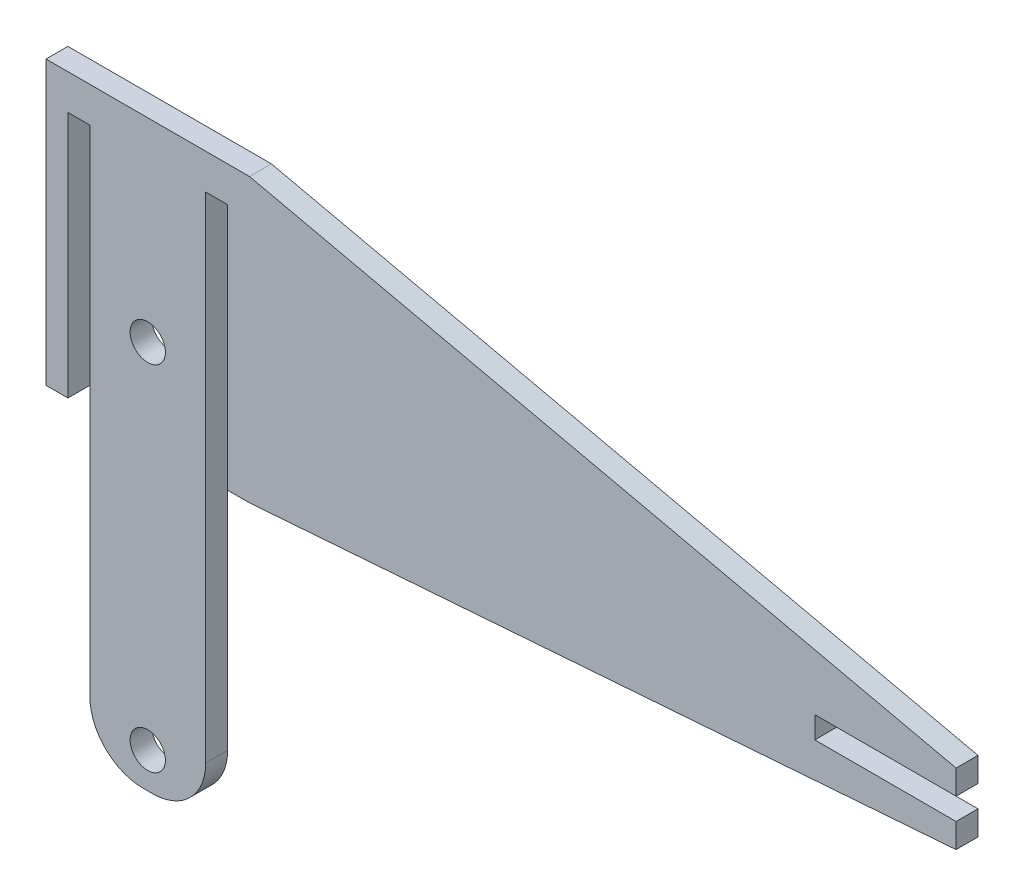
SolidWorks part; units mm, degrees
material "Teak"
ref_plane "Front Plane" through (0, 0, 0) normal (0, 0, 1) x (1, 0, 0)
ref_plane "Top Plane" through (0, 0, 0) normal (0, 1, 0) x (1, 0, 0)
ref_plane "Right Plane" through (0, 0, 0) normal (1, 0, 0) x (0, 0, -1)
sketch "Sketch1" plane through (0, 0, 0) normal (0, 0, 1) x (1, 0, 0)
  line L0 (-14.4, 0) -> (14.4, 0) construction
  line L1 (-14.4, -20) -> (14.4, -20)
  line L2 (-14.4, -20) -> (-14.4, 20)
  line L3 (-14.4, 20) -> (14.4, 20)
  line L4 (14.4, -20) -> (14.4, 20)
  line L5 (-14.4, -20) -> (14.4, 20) construction
  line L6 (-14.4, 20) -> (14.4, -20) construction
  point P0 (0, 0)
  dimension "D1" = 20
  dimension "D2" = 40
  dimension "D3" = 28.8
extrude "Boss-Extrude1" add sketch "Sketch1" along normal blind 3.1 contours L3 L4 L1 L2
sketch "Sketch2" plane through (0, 0, 3.1) normal (0, 0, 1) x (1, 0, 0)
  line L0 (-11.3, -20) -> (-8.2, -20)
  line L1 (-11.3, -20) -> (-11.3, 15)
  line L2 (-8.2, -20) -> (-8.2, 15)
  line L3 (-11.3, 15) -> (-8.2, 15)
  line L4 (-14.4, -20) -> (14.4, -20) construction
  line L5 (-14.4, 20) -> (14.4, 20) construction
  line L6 (0, -20) -> (0, -7.5) construction
  line L7 (11.3, 15) -> (8.2, 15)
  line L8 (8.2, -20) -> (8.2, 15)
  line L9 (11.3, -20) -> (11.3, 15)
  line L10 (11.3, -20) -> (8.2, -20)
  line L11 (-14.4, -20) -> (-14.4, 20) construction
  circle A0 centre (0, -7.5) radius 2.5
  dimension "D4" = 5
  dimension "D1" = 3.1
  dimension "D2" = 3.1
  dimension "D3" = 5
  dimension "D5" = 22.5
extrude "Cut-Extrude1" cut sketch "Sketch2" against normal through all
sketch "Sketch3" plane through (0, 0, 3.1) normal (0, 0, 1) x (1, 0, 0)
  line L0 (-8.2, -20) -> (8.2, -20)
  line L1 (-8.2, -20) -> (-8.2, -62.5)
  line L2 (8.2, -20) -> (8.2, -62.5)
  line L3 (-8.2, -62.5) -> (8.2, -62.5)
  line L4 (-8.2, -20) -> (8.2, -20) construction
  line L5 (-8.2, -20) -> (-8.2, 15) construction
  circle A0 centre (0, -57.5) radius 2.5
  dimension "D2" = 5
  dimension "D1" = 5
  dimension "D3" = 50
extrude "Boss-Extrude2" add sketch "Sketch3" against normal through all
fillet "Fillet1" radius 7.5 2 edges at (8.2, -62.5, 1.55) (-8.2, -62.5, 1.55)
sketch "Sketch4" plane through (0, 0, 0) normal (0, 0, -1) x (-1, 0, 0)
  line L0 (0, -7.5) -> (-43.757, -7.5) construction
  line L1 (-14.4, -20) -> (-14.4, 20) construction
  line L2 (-14.4, 20) -> (-14.4, -20)
  line L3 (-94.4, -9.05) -> (-94.4, -5.95)
  line L4 (-114.4, -12.5) -> (-14.4, -20)
  line L5 (-114.4, -2.5) -> (-14.4, 20)
  line L8 (-43.757, -7.5) -> (-94.4, -7.5) construction
  line L9 (-1.7678, -5.7322) -> (1.7678, -5.7322) construction
  line L10 (-94.4, -5.95) -> (-114.4, -5.95)
  line L11 (0, -5) -> (0, -10) construction
  line L12 (-94.4, -9.05) -> (-114.4, -9.05)
  line L13 (-114.4, -9.05) -> (-114.4, -12.5)
  line L14 (-114.4, -5.95) -> (-114.4, -2.5)
  circle A0 centre (0, -7.5) radius 2.5 construction
  dimension "D3" = 10
  dimension "D1" = 3.1
  dimension "D2" = 0
  dimension "D4" = 3.45
  dimension "D5" = 100
  dimension "D6" = 20
extrude "Boss-Extrude3" add sketch "Sketch4" against normal through all
equation "\"thick\" = 3.1mm"
equation "\"small_bearing_outer\"=12.9mm"
equation "\"servo1_L\"=40.7mm"
equation "\"servo1_W\"=20.5mm"
equation "\"servo1_H\"=43.5mm"
equation "\"servo1_hL\"=49mm"
equation "\"servo1_hW\"=10mm"
equation "\"servo1_H2\"=27mm"
equation "\"D1@Boss-Extrude1\"=\"thick\""
equation "\"D2@Sketch2\"=\"thick\""
equation "\"D1@Sketch3\"=\"D2@Sketch3\""
equation "\"D1@Sketch4\"=\"thick\""
equation "\"D4@Sketch4\"=(\"D3@Sketch4\"-\"D1@Sketch4\")/2"
equation "\"D1@Sketch2\"=\"thick\""
equation "\"D3@Sketch4\"=10"
